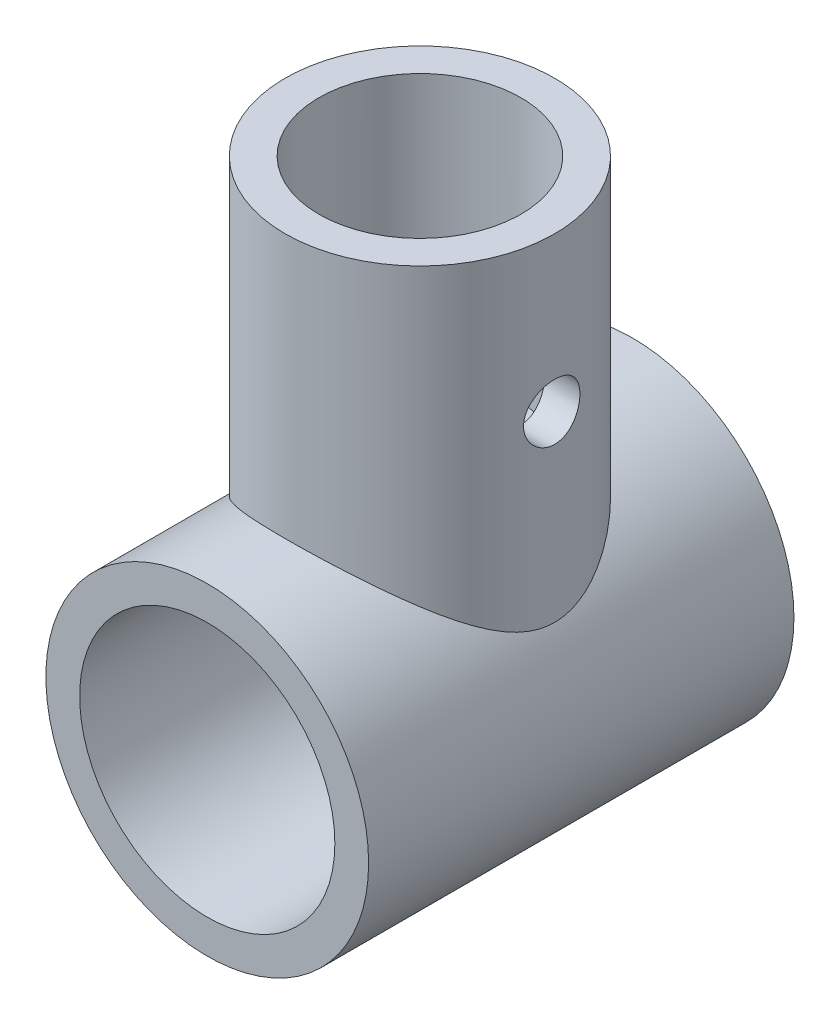
SolidWorks part; units mm, degrees
ref_plane "Front Plane" through (0, 0, 0) normal (0, 0, 1) x (1, 0, 0)
ref_plane "Top Plane" through (0, 0, 0) normal (0, 1, 0) x (1, 0, 0)
ref_plane "Right Plane" through (0, 0, 0) normal (1, 0, 0) x (0, 0, -1)
sketch "Sketch1" plane through (0, 0, 0) normal (0, 0, 1) x (1, 0, 0)
  line L0 (0, 12) -> (0, 15.175) construction
  circle A0 centre (0, 0) radius 12
  circle A1 centre (0, 0) radius 15.175
  dimension "D1" = 24
  dimension "D2" = 3.175
extrude "Boss-Extrude1" add sketch "Sketch1" along normal mid plane 40
ref_plane "Plane4" through (0, 40, 0) normal (0, 1, 0) x (1, 0, 0)
sketch "Sketch2" plane through (0, 40, 0) normal (0, 1, 0) x (1, 0, 0)
  line L0 (0, 9.5) -> (0, 12.675) construction
  circle A0 centre (0, 0) radius 9.5
  circle A1 centre (0, 0) radius 12.675
  dimension "D1" = 19
  dimension "D2" = 3.175
extrude "Boss-Extrude2" add sketch "Sketch2" against normal up to surface (24.825 mm away)
sketch "Sketch3" plane through (0, 0, 0) normal (1, 0, 0) x (0, 0, -1)
  line L0 (0, 40) -> (0, 25.5) construction
  line L1 (16.6925, 40) -> (-16.6925, 40) construction
  line L2 (-20, 0) -> (0, 0) construction
  line L3 (-20, 15.175) -> (-20, -15.175) construction
  dimension "D1" = 14.5
hole_wizard "M5 Clearance Hole1" positions "Sketch4" profile "Sketch5" hole size "M5" standard "ANSI Metric"
sketch "Sketch4" plane through (0, 0, 0) normal (1, 0, 0) x (0, 0, -1)
  point P6 (0, 25.5)
sketch "Sketch5" plane through (0, 25.5, 0) normal (0, 1, 0) x (0, 0, 1)
  line L0 (0, 0) -> (0, 15.175)
  line L1 (0, 15.175) -> (2.65, 15.175)
  line L2 (2.65, 15.175) -> (2.65, 0)
  line L5 (2.65, 0) -> (0, 0)
  line L11 (0, -6.35) -> (0, 107.95) construction
  dimension "Thru Hole Dia." = 5.3
  dimension "Thru Hole Depth" = 15.175
mirror "Mirror1" about plane through (0, 0, 0) normal (1, 0, 0) of "M5 Clearance Hole1"
equation "\"tubeOutDiameter\" = 35mm"
equation "\"wheelShaftDiameter\"= 12mm"
equation "\"wheelThickness\"= 135mm"
equation "\"BearingDiameter\"= 20mm"
equation "\"BearingThickness\"= 10mm"
equation "\"frontShaftDiameter\"= 20mm"
equation "\"D1@Sketch1\"=\"wheelShaftDiameter\"*2"
